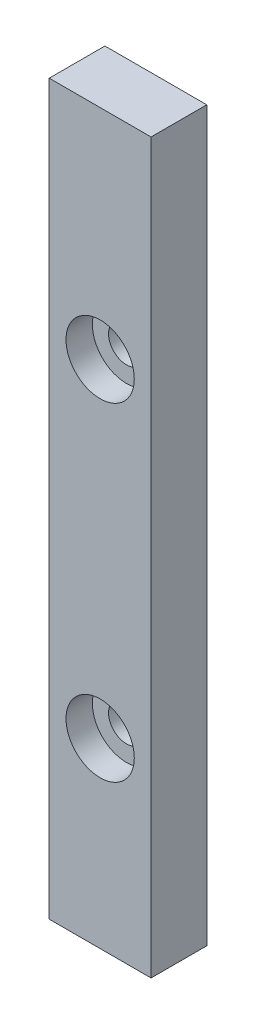
SolidWorks part; units mm, degrees
material "6061-T6 (SS)"
ref_plane "Front Plane" through (0, 0, 0) normal (0, 0, 1) x (1, 0, 0)
ref_plane "Top Plane" through (0, 0, 0) normal (0, 1, 0) x (1, 0, 0)
ref_plane "Right Plane" through (0, 0, 0) normal (1, 0, 0) x (0, 0, -1)
sketch "Sketch1" plane through (0, 0, 0) normal (0, 0, 1) x (1, 0, 0)
  line L1 (0, 0) -> (8.5, 0)
  line L2 (0, 0) -> (0, -60.8)
  line L3 (0, -60.8) -> (8.5, -60.8)
  line L4 (8.5, 0) -> (8.5, -60.8)
  dimension "D1" = 60.8
  dimension "D2" = 8.5
extrude "Boss-Extrude1" add sketch "Sketch1" along normal blind 4.65
sketch "Sketch3" plane through (0, 0, 4.65) normal (0, 0, 1) x (1, 0, 0)
  line L0 (8.5, 0) -> (0, 0) construction
  line L4 (8.5, -60.8) -> (8.5, 0) construction
  point P9 (4.25, -18.2)
  point P10 (4.25, -45.6)
  dimension "D1" = 18.2
  dimension "D2" = 27.4
  dimension "D3" = 4.25
  dimension "D4" = 4.25
hole_wizard "Ø3.0mm Dowel Hole1" positions "Sketch4" profile "Sketch5" hole size "Ø3.0" standard "ANSI Metric"
sketch "Sketch4" plane through (0, 0, 4.65) normal (0, 0, 1) x (1, 0, 0)
  point P0 (4.25, -18.2)
  point P3 (4.25, -45.6)
sketch "Sketch5" plane through (4.25, -18.2, 4.65) normal (1, 0, 0) x (0, -1, 0)
  line L0 (0, 0) -> (0, 5.9013)
  line L1 (0, 5.9013) -> (1.5, 5)
  line L2 (1.5, 5) -> (1.5, 0)
  line L5 (1.5, 0) -> (0, 0)
  line L10 (0, 5.9013) -> (-1.5, 5) construction
  line L11 (0, -6.35) -> (0, 107.95) construction
  dimension "Hole Dia." = 3
  dimension "Hole Depth" = 5
  dimension "Drill Angle" = 118
sketch "Sketch6" plane through (0, 0, 4.65) normal (0, 0, 1) x (1, 0, 0)
  circle A0 centre (4.25, -18.2) radius 2.85
  circle A1 centre (4.25, -45.6) radius 2.85
  dimension "D1" = 5.7
extrude "Cut-Extrude1" cut sketch "Sketch6" against normal blind 2.2
